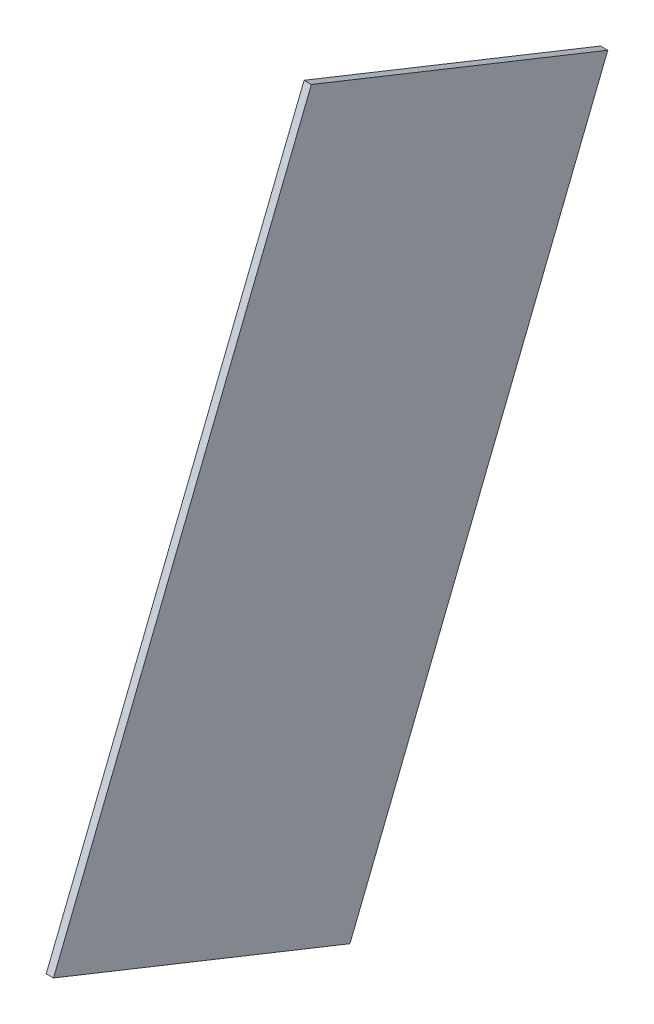
SolidWorks part; units mm, degrees
ref_plane "Front Plane" through (0, 0, 0) normal (0, 0, 1) x (1, 0, 0)
ref_plane "Top Plane" through (0, 0, 0) normal (0, 1, 0) x (1, 0, 0)
ref_plane "Right Plane" through (0, 0, 0) normal (1, 0, 0) x (0, 0, -1)
sketch "Sketch2" plane through (0, 51.3184, -20.5196) normal (0, -0.9285, 0.3713) x (-1, 0, 0)
  line L0 (-0.8354, 1694.702) -> (-3.8354, 1694.702)
  line L2 (-3.8354, 1694.702) -> (-3.8354, 1825.702)
  line L11 (-0.8354, 1825.702) -> (-0.8354, 1694.702)
  line L13 (-0.8354, 1825.702) -> (-3.8354, 1825.702)
  circle A1 centre (61.6646, 1760.202) radius 65.5 construction
  dimension "D1" = 3
extrude "Boss-Extrude1" add sketch "Sketch2" along normal up to surface (285 mm away) contours L13 L2 L0 L11
